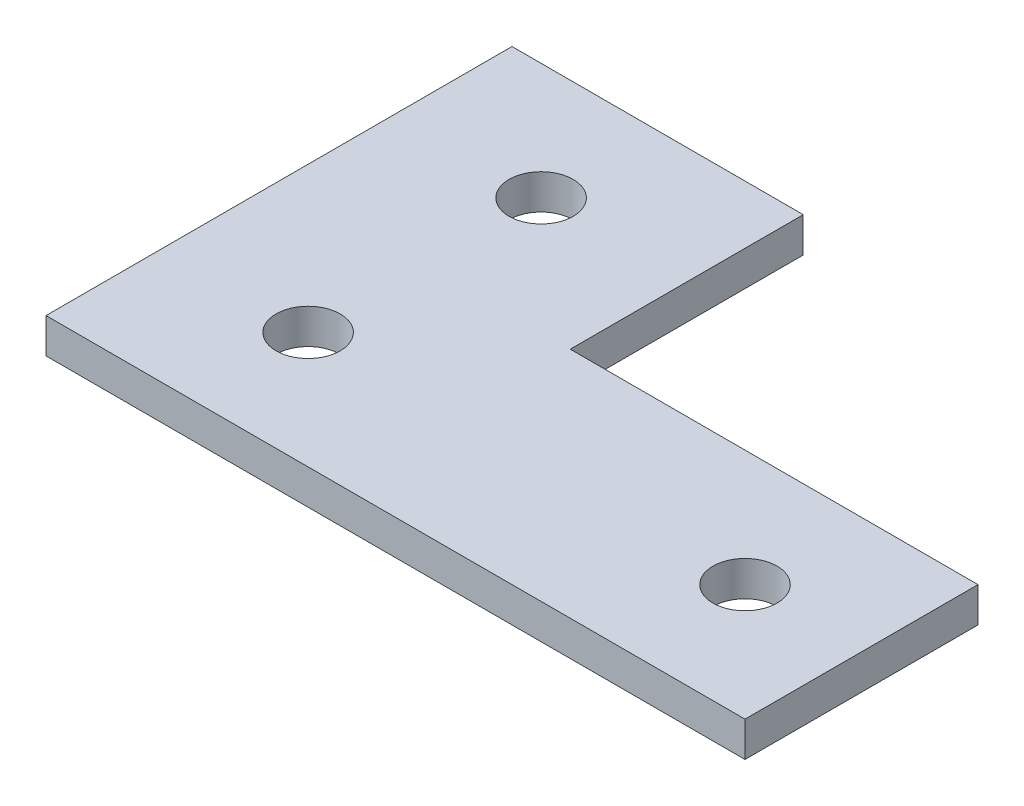
SolidWorks part; units mm, degrees
ref_plane "Front Plane" through (0, 0, 0) normal (0, 0, 1) x (1, 0, 0)
ref_plane "Top Plane" through (0, 0, 0) normal (0, 1, 0) x (1, 0, 0)
ref_plane "Right Plane" through (0, 0, 0) normal (1, 0, 0) x (0, 0, -1)
sketch "Sketch1" plane through (0, 0, 0) normal (0, 1, 0) x (1, 0, 0)
  line L1 (0, 0) -> (25, 0)
  line L2 (0, 0) -> (0, -40)
  line L3 (0, -40) -> (25, -40)
  line L4 (25, 0) -> (25, -40)
  line L5 (25, -40) -> (60, -40)
  line L6 (25, -40) -> (25, -20)
  line L7 (25, -20) -> (60, -20)
  line L8 (60, -40) -> (60, -20)
  dimension "D1" = 25
  dimension "D2" = 40
  dimension "D3" = 35
  dimension "D4" = 20
extrude "Boss-Extrude1" add sketch "Sketch1" along normal blind 3 contours L4 L1 L2 L3 | L5 L8 L7 L4
sketch "Sketch4" plane through (0, 3, 0) normal (0, 1, 0) x (1, 0, 0)
  line L0 (12.5, 0) -> (12.5, -40) construction
  line L1 (0, 0) -> (25, 0) construction
  line L2 (0, -40) -> (60, -40) construction
  line L3 (60, -30) -> (0, -30) construction
  line L6 (60, -40) -> (60, -20) construction
  circle A0 centre (12.5, -10) radius 2.75
  circle A1 centre (12.5, -30) radius 2.75
  circle A2 centre (50, -30) radius 2.75
  point P16 (0, 0)
  dimension "D2" = 5.5
  dimension "D3" = 5.5
  dimension "D5" = 5.5
  dimension "D1" = 10
  dimension "D4" = 20
  dimension "D6" = 10
extrude "Cut-Extrude1" cut sketch "Sketch4" against normal blind 3
